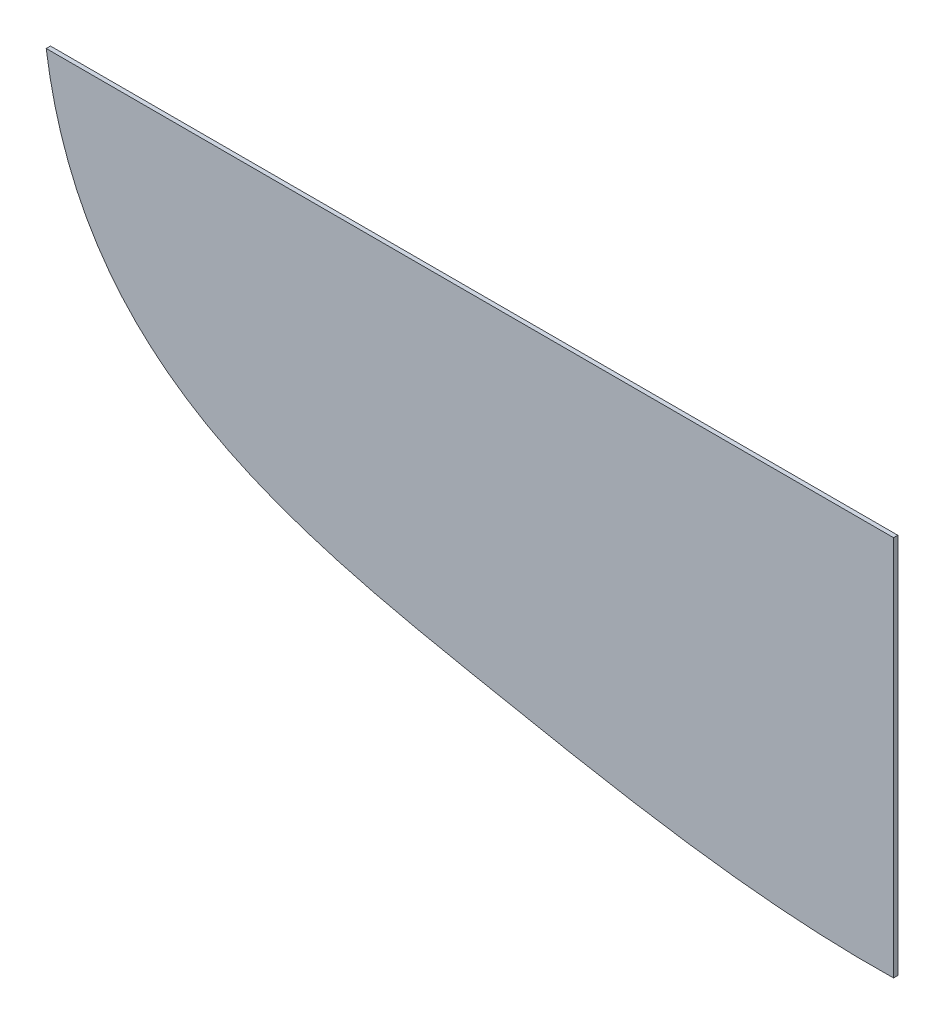
SolidWorks part; units mm, degrees
ref_plane "前视基准面" through (0, 0, 0) normal (0, 0, 1) x (1, 0, 0)
ref_plane "上视基准面" through (0, 0, 0) normal (0, 1, 0) x (1, 0, 0)
ref_plane "右视基准面" through (0, 0, 0) normal (1, 0, 0) x (0, 0, -1)
sketch "草图1" plane through (0, 0, 0) normal (0, 0, 1) x (1, 0, 0)
  line L0 (0, 0) -> (0, -18)
  line L1 (0, 0) -> (-40, 0)
  spline S0 degree 3 poles (-40, 0) (-38.3307, -11.7944) (-21.604, -15.2109) (-6.5771, -18.1297) (0, -18) knots 0 0 0 0 0.585812 1 1 1 1
  dimension "D1" = 40
  dimension "D2" = 18
extrude "凸台-拉伸1" add sketch "草图1" along normal mid plane 0.2
sketch "草图2" plane through (0, 0, 0) normal (0, 1, 0) x (1, 0, 0)
  line L0 (0, -0.1) -> (0, -2.5689)
  line L1 (0, -0.1) -> (-40, -0.1) construction
sketch "草图3" plane through (0, 0, 0) normal (0, 1, 0) x (1, 0, 0)
  line L0 (0, 0) -> (-40, 0) construction
  line L1 (-40, -0.1) -> (-40, 0.1) construction
